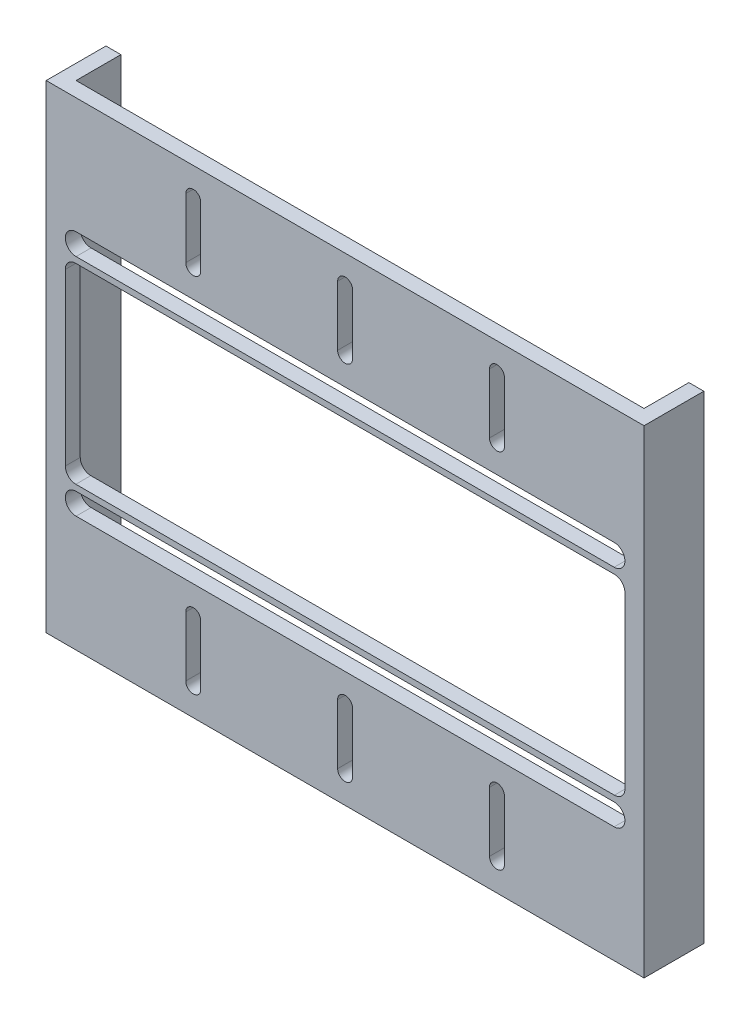
SolidWorks part; units mm, degrees
material "1060 Alloy"
ref_plane "Front Plane" through (0, 0, 0) normal (0, 0, 1) x (1, 0, 0)
ref_plane "Top Plane" through (0, 0, 0) normal (0, 1, 0) x (1, 0, 0)
ref_plane "Right Plane" through (0, 0, 0) normal (1, 0, 0) x (0, 0, -1)
sketch "Sketch2" plane through (0, 0, 0) normal (0, 1, 0) x (1, 0, 0)
  line L0 (0, 0) -> (0, 12.7)
  line L1 (0, 12.7) -> (3.175, 12.7)
  line L2 (3.175, 12.7) -> (3.175, 3.175)
  line L3 (3.175, 3.175) -> (123.825, 3.175)
  line L4 (123.825, 3.175) -> (123.825, 12.7)
  line L5 (123.825, 12.7) -> (127, 12.7)
  line L6 (127, 12.7) -> (127, 0)
  line L7 (127, 0) -> (0, 0)
  dimension "D1" = 127
  dimension "D2" = 12.7
  dimension "D3" = 3.175
  dimension "D4" = 9.525
extrude "Boss-Extrude1" add sketch "Sketch2" along normal blind 139.7
sketch "Sketch3" plane through (0, 0, -3.175) normal (0, 0, -1) x (-1, 0, 0)
  line L0 (-6.35, 112.776) -> (-120.65, 112.776) construction
  line L1 (-6.35, 110.49) -> (-120.65, 110.49)
  line L2 (-6.35, 115.062) -> (-120.65, 115.062)
  line L3 (-6.35, 65.024) -> (-120.65, 65.024) construction
  line L4 (-6.35, 62.738) -> (-120.65, 62.738)
  line L5 (-6.35, 67.31) -> (-120.65, 67.31)
  line L6 (-120.65, 112.776) -> (-120.65, 65.024) construction
  line L7 (-6.35, 112.776) -> (-6.35, 65.024) construction
  line L8 (-6.35, 88.9) -> (0, 88.9) construction
  line L9 (0, 139.7) -> (0, 0) construction
  line L10 (-120.65, 88.9) -> (-127, 88.9) construction
  line L11 (-127, 139.7) -> (-127, 0) construction
  line L13 (-122.936, 112.776) -> (-122.936, 65.024) construction
  line L14 (-4.064, 109.22) -> (-122.936, 109.22)
  line L15 (-4.064, 109.22) -> (-4.064, 68.58)
  line L16 (-4.064, 68.58) -> (-122.936, 68.58)
  line L17 (-122.936, 109.22) -> (-122.936, 68.58)
  line L18 (-4.064, 112.776) -> (-4.064, 65.024) construction
  line L19 (-29.703, 109.22) -> (-29.703, 112.776) construction
  line L20 (-30.3502, 65.024) -> (-30.3502, 68.58) construction
  line L21 (-120.65, 112.776) -> (-120.65, 139.7) construction
  line L22 (0, 139.7) -> (-127, 139.7) construction
  line L23 (-120.65, 65.024) -> (-120.65, 38.1) construction
  line L25 (0, 38.1) -> (0, 0)
  line L26 (0, 0) -> (-127, 0)
  line L27 (-127, 0) -> (-127, 38.1)
  line L28 (-127, 38.1) -> (0, 38.1)
  arc A0 (-6.35, 110.49) -> (-6.35, 115.062) centre (-6.35, 112.776) ccw
  arc A1 (-120.65, 115.062) -> (-120.65, 110.49) centre (-120.65, 112.776) ccw
  arc A2 (-6.35, 62.738) -> (-6.35, 67.31) centre (-6.35, 65.024) ccw
  arc A3 (-120.65, 67.31) -> (-120.65, 62.738) centre (-120.65, 65.024) ccw
  point P2 (-63.5, 112.776)
  point P7 (-63.5, 65.024)
  dimension "D2" = 2.286
  dimension "D1" = 40.64
  dimension "D3" = 47.752
  dimension "D5" = 6.35
  dimension "D6" = 38.1
extrude "Cut-Extrude1" cut sketch "Sketch3" against normal through all both and the other way through all
fillet "Fillet1" radius 2.2352 4 edges at (4.064, 68.58, -1.5875) (4.064, 109.22, -1.5875) (122.936, 68.58, -1.5875) (122.936, 109.22, -1.5875)
sketch "Sketch4" plane through (0, 0, 0) normal (0, 0, 1) x (1, 0, 0)
  line L0 (31.242, 133.731) -> (31.242, 121.031) construction
  line L1 (32.8295, 133.731) -> (32.8295, 121.031)
  line L2 (29.6545, 133.731) -> (29.6545, 121.031)
  line L3 (31.242, 56.769) -> (31.242, 44.069) construction
  line L4 (32.8295, 56.769) -> (32.8295, 44.069)
  line L5 (29.6545, 56.769) -> (29.6545, 44.069)
  line L6 (61.9125, 133.731) -> (61.9125, 121.031)
  line L7 (65.0875, 133.731) -> (65.0875, 121.031)
  line L8 (61.9125, 56.769) -> (61.9125, 44.069)
  line L9 (65.0875, 56.769) -> (65.0875, 44.069)
  line L10 (63.5, 133.731) -> (63.5, 121.031) construction
  line L11 (63.5, 56.769) -> (63.5, 44.069) construction
  line L12 (94.1705, 133.731) -> (94.1705, 121.031)
  line L13 (97.3455, 133.731) -> (97.3455, 121.031)
  line L14 (94.1705, 56.769) -> (94.1705, 44.069)
  line L15 (97.3455, 56.769) -> (97.3455, 44.069)
  line L16 (95.758, 133.731) -> (95.758, 121.031) construction
  line L17 (95.758, 56.769) -> (95.758, 44.069) construction
  line L19 (31.242, 127.381) -> (63.5, 127.381) construction
  line L20 (63.5, 127.381) -> (95.758, 127.381) construction
  line L21 (95.758, 127.381) -> (127, 127.381) construction
  line L22 (127, 139.7) -> (127, 38.1) construction
  line L23 (31.242, 127.381) -> (0, 127.381) construction
  line L24 (0, 139.7) -> (0, 38.1) construction
  line L25 (31.242, 50.419) -> (63.5, 50.419) construction
  line L26 (63.5, 50.419) -> (95.758, 50.419) construction
  line L27 (95.758, 50.419) -> (127, 50.419) construction
  line L28 (31.242, 50.419) -> (0, 50.419) construction
  line L29 (8.9758, 127.381) -> (8.9758, 139.7) construction
  line L30 (0, 139.7) -> (127, 139.7) construction
  line L31 (8.9758, 127.381) -> (8.9758, 115.062) construction
  line L32 (6.35, 115.062) -> (120.65, 115.062) construction
  line L33 (21.5915, 38.1) -> (21.5915, 50.419) construction
  line L34 (127, 38.1) -> (0, 38.1) construction
  arc A0 (32.8295, 133.731) -> (29.6545, 133.731) centre (31.242, 133.731) ccw
  arc A1 (29.6545, 121.031) -> (32.8295, 121.031) centre (31.242, 121.031) ccw
  arc A2 (32.8295, 56.769) -> (29.6545, 56.769) centre (31.242, 56.769) ccw
  arc A3 (29.6545, 44.069) -> (32.8295, 44.069) centre (31.242, 44.069) ccw
  arc A4 (65.0875, 133.731) -> (61.9125, 133.731) centre (63.5, 133.731) ccw
  arc A5 (61.9125, 121.031) -> (65.0875, 121.031) centre (63.5, 121.031) ccw
  arc A6 (65.0875, 56.769) -> (61.9125, 56.769) centre (63.5, 56.769) ccw
  arc A7 (61.9125, 44.069) -> (65.0875, 44.069) centre (63.5, 44.069) ccw
  arc A8 (97.3455, 133.731) -> (94.1705, 133.731) centre (95.758, 133.731) ccw
  arc A9 (94.1705, 121.031) -> (97.3455, 121.031) centre (95.758, 121.031) ccw
  arc A10 (97.3455, 56.769) -> (94.1705, 56.769) centre (95.758, 56.769) ccw
  arc A11 (94.1705, 44.069) -> (97.3455, 44.069) centre (95.758, 44.069) ccw
  point P2 (31.242, 127.381)
  point P7 (31.242, 50.419)
  point P18 (63.5, 127.381)
  point P23 (63.5, 50.419)
  point P32 (95.758, 127.381)
  point P37 (95.758, 50.419)
  dimension "D4" = 1.5875
  dimension "D1" = 12.7
  dimension "D2" = 3
  dimension "D3" = 32.258
extrude "Cut-Extrude2" cut sketch "Sketch4" against normal through all
